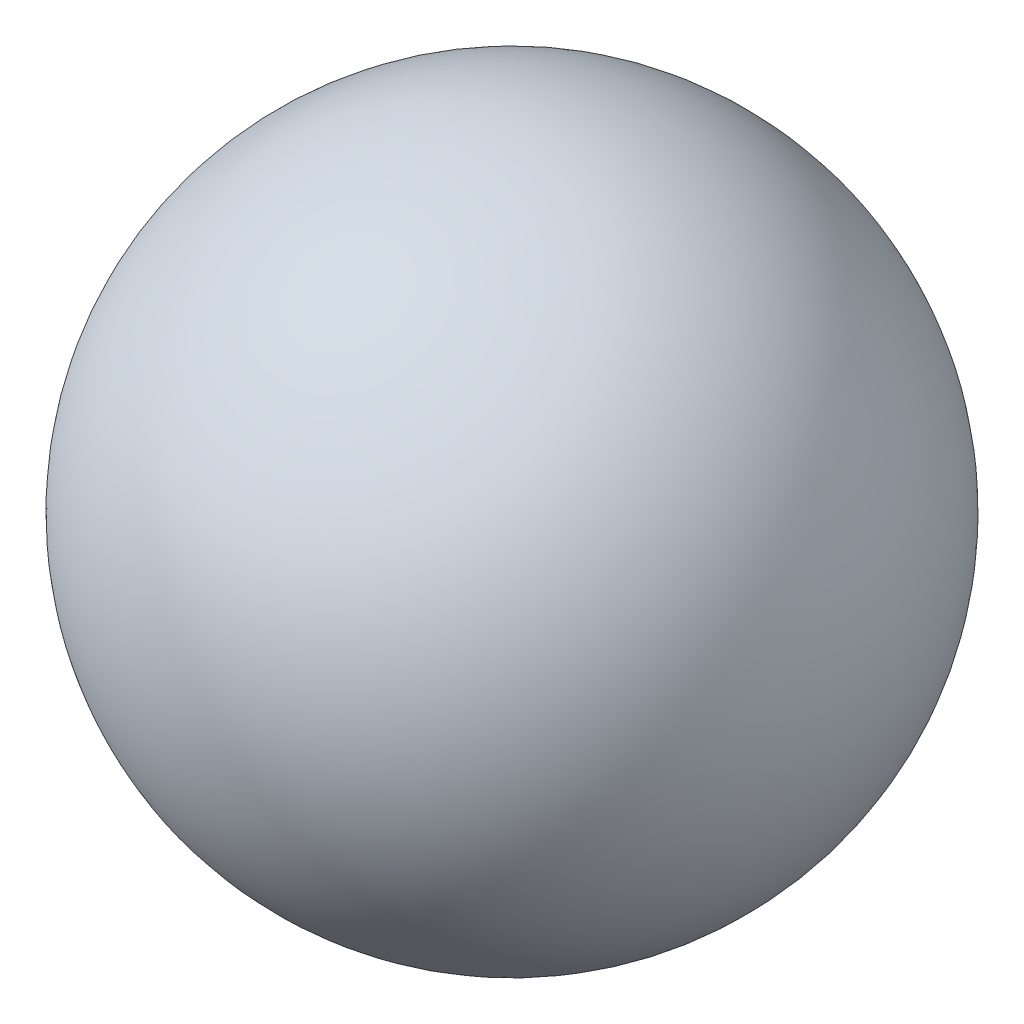
SolidWorks part; units mm, degrees
material "Custom Plastic"
ref_plane "Front Plane" through (0, 0, 0) normal (0, 0, 1) x (1, 0, 0)
ref_plane "Top Plane" through (0, 0, 0) normal (0, 1, 0) x (1, 0, 0)
ref_plane "Right Plane" through (0, 0, 0) normal (1, 0, 0) x (0, 0, -1)
sketch "Sketch1" plane through (0, 0, 0) normal (0, 1, 0) x (1, 0, 0)
  line L0 (0, 0) -> (0, -177.8)
  arc A1 (0, 0) -> (0, -177.8) centre (0, -88.9) ccw
  dimension "D1" = 177.8
revolve "Revolve1" add sketch "Sketch1" angle 360 about L0
